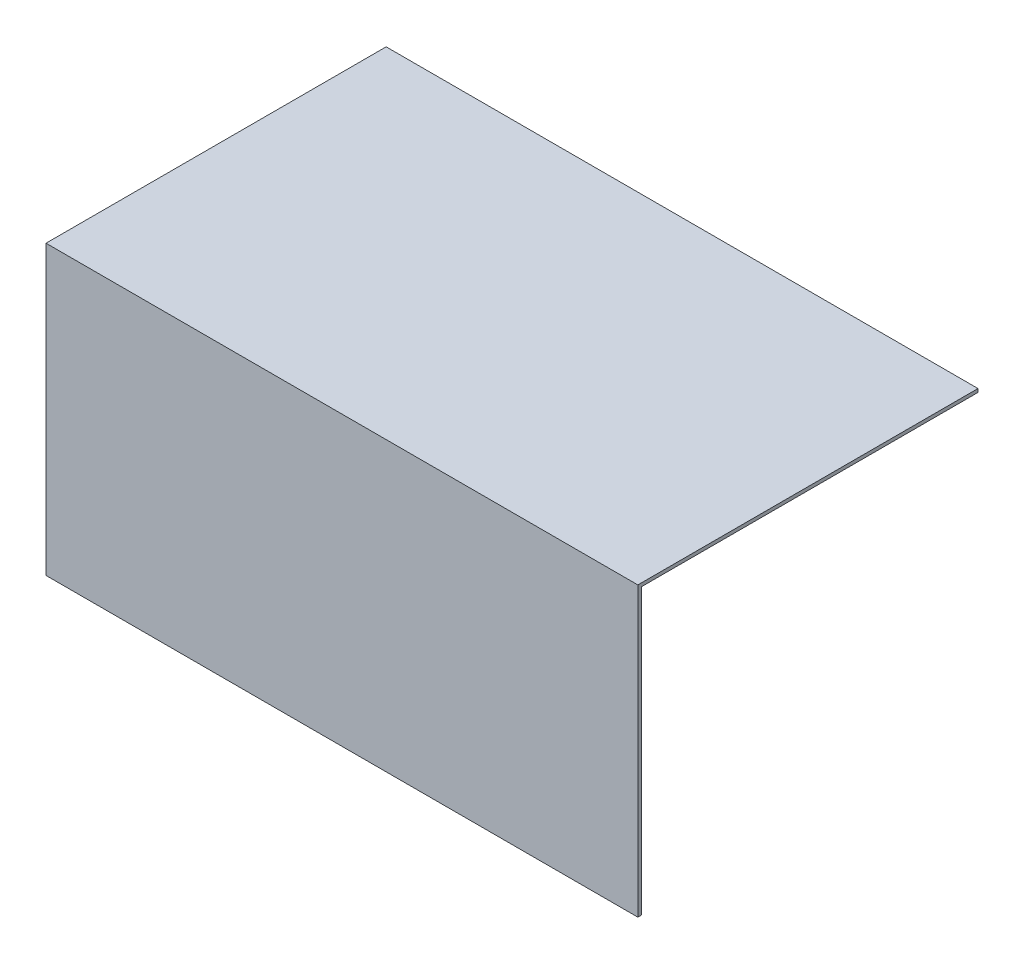
SolidWorks part; units mm, degrees
ref_plane "Plan de face" through (0, 0, 0) normal (0, 0, 1) x (1, 0, 0)
ref_plane "Plan de dessus" through (0, 0, 0) normal (0, 1, 0) x (1, 0, 0)
ref_plane "Plan de droite" through (0, 0, 0) normal (1, 0, 0) x (0, 0, -1)
sketch "Esquisse1" plane through (0, 0, 0) normal (0, 0, 1) x (1, 0, 0)
  line L3 (17.5095, 24.0269) -> (-40.4905, 24.0269)
  line L4 (17.5095, 24.0269) -> (17.5095, -60.5731)
  line L5 (17.5095, -60.5731) -> (-40.4905, -60.5731)
  line L6 (-40.4905, 24.0269) -> (-40.4905, -60.5731)
  dimension "D1" = 58
  dimension "D2" = 84.6
extrude "Boss.-Extru.1" add sketch "Esquisse1" along normal blind 1
sketch "Esquisse2" plane through (0, 0, 0) normal (0, 0, -1) x (-1, 0, 0)
  line L0 (40.4905, 24.0269) -> (40.4905, -60.5731) construction
  line L1 (-17.5095, 24.0269) -> (40.4905, 24.0269)
  line L2 (-17.5095, 24.0269) -> (-17.5095, 23.0269)
  line L3 (-17.5095, 23.0269) -> (40.4905, 23.0269)
  line L4 (40.4905, 24.0269) -> (40.4905, 23.0269)
  dimension "D1" = 1
extrude "Boss.-Extru.2" add sketch "Esquisse2" along normal blind 99
sketch "Esquisse3" plane through (17.5095, 0, 0) normal (1, 0, 0) x (0, 0, -1)
  line L0 (99, 24.0269) -> (99, 23.0269)
  line L1 (99, 23.0269) -> (0, 23.0269)
  line L2 (0, 23.0269) -> (0, -60.5731)
  line L3 (0, -60.5731) -> (-1, -60.5731)
  line L4 (-1, -60.5731) -> (-1, 24.0269)
  line L5 (-1, 24.0269) -> (99, 24.0269)
extrude "Boss.-Extru.3" add sketch "Esquisse3" along normal blind 116
